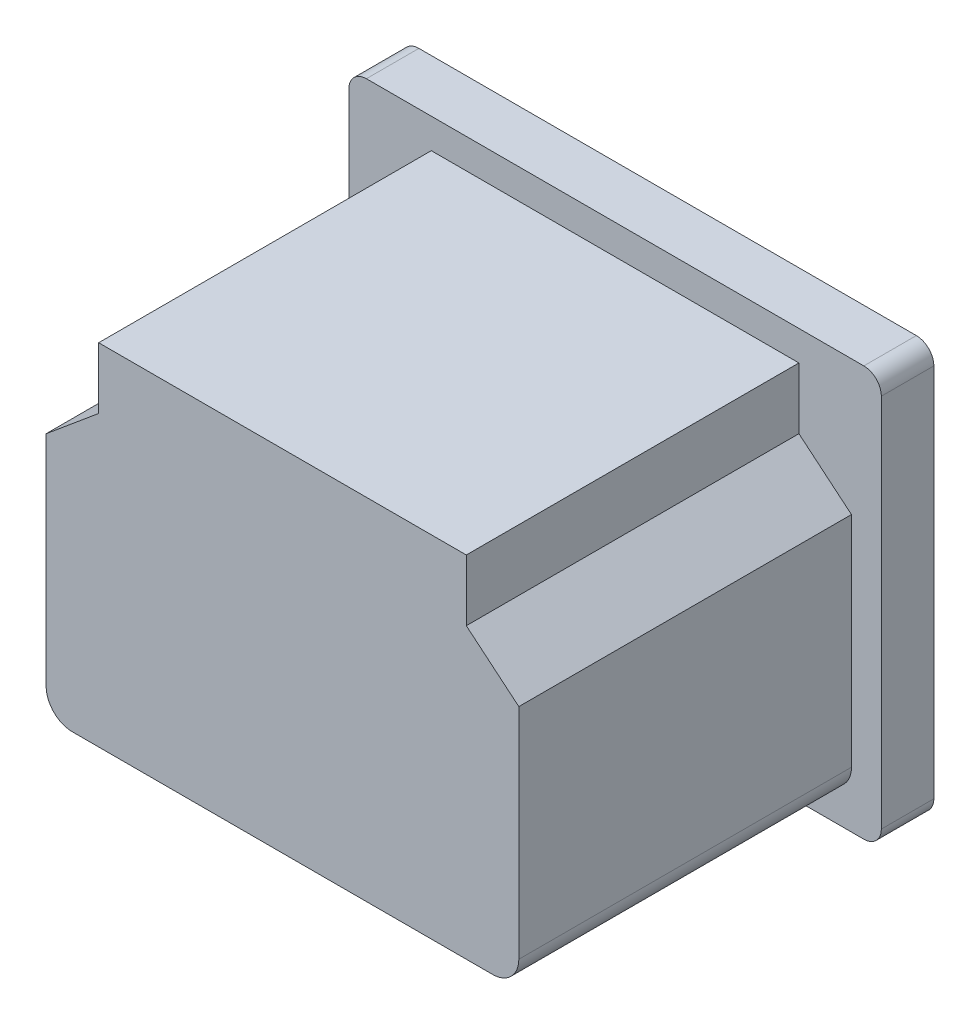
SolidWorks part; units mm, degrees
ref_plane "前视基准面" through (0, 0, 0) normal (0, 0, 1) x (1, 0, 0)
ref_plane "上视基准面" through (0, 0, 0) normal (0, 1, 0) x (1, 0, 0)
ref_plane "右视基准面" through (0, 0, 0) normal (1, 0, 0) x (0, 0, -1)
sketch "草图1" plane through (0, 0, 0) normal (0, 0, 1) x (1, 0, 0)
  line L0 (0, 13.7201) -> (0, -13.5947) construction
  line L1 (-14.2071, 11.7071) -> (14.2071, 11.7071)
  line L2 (-15.2071, 10.7071) -> (-15.2071, -10.7071)
  line L3 (-14.2071, -11.7071) -> (14.2071, -11.7071)
  line L4 (15.2071, 10.7071) -> (15.2071, -10.7071)
  line L5 (-14.8758, 11.4506) -> (14.8758, -11.4506) construction
  line L6 (-14.8758, -11.4506) -> (14.8758, 11.4506) construction
  line L7 (-17.9891, 0) -> (17.1703, 0) construction
  arc A0 (14.2071, 11.7071) -> (15.2071, 10.7071) centre (14.2071, 10.7071) cw
  arc A1 (-14.2071, 11.7071) -> (-15.2071, 10.7071) centre (-14.2071, 10.7071) ccw
  arc A2 (14.2071, -11.7071) -> (15.2071, -10.7071) centre (14.2071, -10.7071) ccw
  arc A3 (-14.2071, -11.7071) -> (-15.2071, -10.7071) centre (-14.2071, -10.7071) cw
  point P0 (0, 0)
  point P13 (-14.9142, 11.4142)
  dimension "D3" = 1
extrude "凸台-拉伸1" add sketch "草图1" along normal blind 3
sketch "草图2" plane through (0, 0, 3) normal (0, 0, 1) x (1, 0, 0)
  line L0 (-10.5, 10) -> (-10.5, 6.5)
  line L1 (-13.5, 10) -> (13.5, 10) construction
  line L2 (-13.5, 10) -> (-13.5, -8.5) construction
  line L3 (-12, -10) -> (12, -10)
  line L4 (13.5, 10) -> (13.5, -8.5) construction
  line L5 (-13.5, 10) -> (13.5, -10) construction
  line L6 (-13.5, -10) -> (13.5, 10) construction
  line L7 (-10.5, 6.5) -> (-13.5, 4)
  line L8 (0, 0) -> (0, 13.5753) construction
  line L9 (10.5, 6.5) -> (13.5, 4)
  line L10 (10.5, 10) -> (10.5, 6.5)
  line L11 (-10.5, 10) -> (10.5, 10)
  line L12 (13.5, 4) -> (13.5, -8.5)
  line L13 (-13.5, -8.5) -> (-13.5, 4)
  arc A0 (12, -10) -> (13.5, -8.5) centre (12, -8.5) ccw
  arc A1 (-13.5, -8.5) -> (-12, -10) centre (-12, -8.5) ccw
  point P0 (0, 0)
  dimension "D3" = 1.5
  dimension "D1" = 27
  dimension "D2" = 20
  dimension "D4" = 3
  dimension "D5" = 3.5
  dimension "D6" = 6
extrude "凸台-拉伸2" add sketch "草图2" along normal blind 19
sketch "草图3" plane through (0, 0, 0) normal (0, 0, -1) x (-1, 0, 0)
  line L0 (-19.2665, -0.0256) -> (17.6765, -0.0256) construction
  line L1 (12, -6.5256) -> (12, 1.7613)
  line L2 (11.8463, 2.1219) -> (5.8951, 7.8351)
  line L3 (5.5488, 7.9744) -> (-5.5488, 7.9744)
  line L4 (-5.8951, 7.8351) -> (-11.8463, 2.1219)
  line L5 (-12, 1.7613) -> (-12, -6.5256)
  line L6 (-10.5, -8.0256) -> (10.5, -8.0256)
  line L7 (0, 11.4102) -> (0, -12.252) construction
  arc A0 (12, -6.5256) -> (10.5, -8.0256) centre (10.5, -6.5256) cw
  arc A1 (-12, -6.5256) -> (-10.5, -8.0256) centre (-10.5, -6.5256) ccw
  arc A2 (5.8951, 7.8351) -> (5.5488, 7.9744) centre (5.5488, 7.4744) ccw
  arc A3 (12, 1.7613) -> (11.8463, 2.1219) centre (11.5, 1.7613) ccw
  arc A4 (-11.8463, 2.1219) -> (-12, 1.7613) centre (-11.5, 1.7613) ccw
  arc A5 (-5.5488, 7.9744) -> (-5.8951, 7.8351) centre (-5.5488, 7.4744) ccw
  point P19 (5.75, 7.9744)
  point P25 (-12, -8.0256)
  point P29 (-12, 1.9744)
  point P32 (-5.75, 7.9744)
  dimension "D5" = 1.5
  dimension "D6" = 0.5
  dimension "D1" = 24
  dimension "D2" = 16
  dimension "D3" = 11.5
  dimension "D4" = 10
extrude "切除-拉伸1" cut sketch "草图3" against normal blind 17.5 contours L1 A3 L2 A2 L3 A5 L4 A4 L5 A1 L6 A0
sketch "草图4" plane through (0, 0, 17.5) normal (0, 0, -1) x (-1, 0, 0)
  line L0 (-10.5, -8.0256) -> (10.5, -8.0256) construction
  line L1 (-7, -4.0415) -> (7, -4.0415) construction
  line L2 (7, -4.0415) -> (0, 3.1) construction
  line L3 (0, 3.1) -> (-7, -4.0415) construction
  line L4 (0, -9.3874) -> (0, 7.3477) construction
  line L5 (-8, -2.0415) -> (-6, -2.0415)
  line L6 (-8, -2.0415) -> (-8, -6.0415)
  line L7 (-8, -6.0415) -> (-6, -6.0415)
  line L8 (-6, -2.0415) -> (-6, -6.0415)
  line L9 (-8, -2.0415) -> (-6, -6.0415) construction
  line L10 (-8, -6.0415) -> (-6, -2.0415) construction
  line L11 (-1, 5.1) -> (1, 5.1)
  line L12 (-1, 5.1) -> (-1, 1.1)
  line L13 (-1, 1.1) -> (1, 1.1)
  line L14 (1, 5.1) -> (1, 1.1)
  line L15 (-1, 5.1) -> (1, 1.1) construction
  line L16 (-1, 1.1) -> (1, 5.1) construction
  line L17 (8, -6.0415) -> (6, -6.0415)
  line L18 (6, -2.0415) -> (6, -6.0415)
  line L19 (8, -2.0415) -> (6, -2.0415)
  line L20 (8, -2.0415) -> (8, -6.0415)
  dimension "D1" = 14
  dimension "D2" = 10
  dimension "D3" = 4
  dimension "D4" = 2
  dimension "D5" = 2
  dimension "D6" = 4
extrude "凸台-拉伸3" add sketch "草图4" along normal blind 12.5
sketch "草图5" plane through (0, 1.1, 0) normal (0, -1, 0) x (1, 0, 0)
  line L0 (1, 5) -> (-1, 5)
  line L1 (-1, 5) -> (-0.5, 2.5)
  line L2 (-0.5, 2.5) -> (0.5, 2.5)
  line L3 (0.5, 2.5) -> (1, 5)
  line L4 (1, 17.5) -> (-1, 17.5)
  line L5 (-1, 17.5) -> (-1, 5)
  line L6 (-1, 5) -> (1, 5)
  line L7 (1, 5) -> (1, 17.5)
  line L10 (-1, 5) -> (1, 5) construction
  dimension "D2" = 2.5
  dimension "D3" = 1
  dimension "D1" = 0
extrude "凸台-拉伸4" add sketch "草图5" against normal blind 4
sketch "草图6" plane through (0, -6.0415, 0) normal (0, -1, 0) x (1, 0, 0)
  line L0 (8, 5) -> (8, 7.5)
  line L1 (8, 7.5) -> (7.5, 5)
  line L2 (7.5, 5) -> (8, 5)
  line L3 (7, 5.1228) -> (7, 9.6911) construction
  line L4 (8, 17.5) -> (6, 17.5)
  line L5 (6, 17.5) -> (6, 5)
  line L6 (6, 5) -> (8, 5)
  line L7 (8, 5) -> (8, 17.5)
  line L10 (6, 5) -> (8, 5) construction
  line L12 (6.5, 5) -> (6, 5)
  line L13 (6, 7.5) -> (6.5, 5)
  line L14 (6, 5) -> (6, 7.5)
  line L15 (0, -2.153) -> (0, 19.8012) construction
  line L16 (-6, 5) -> (-8, 5) construction
  line L17 (-6, 5) -> (-6, 7.5)
  line L18 (-6, 7.5) -> (-6.5, 5)
  line L19 (-6.5, 5) -> (-6, 5)
  line L20 (-7.5, 5) -> (-8, 5)
  line L21 (-8, 7.5) -> (-7.5, 5)
  line L22 (-8, 5) -> (-8, 7.5)
  dimension "D2" = 2.5
  dimension "D3" = 0.5
  dimension "D1" = 0
extrude "切除-拉伸2" cut sketch "草图6" against normal blind 4
